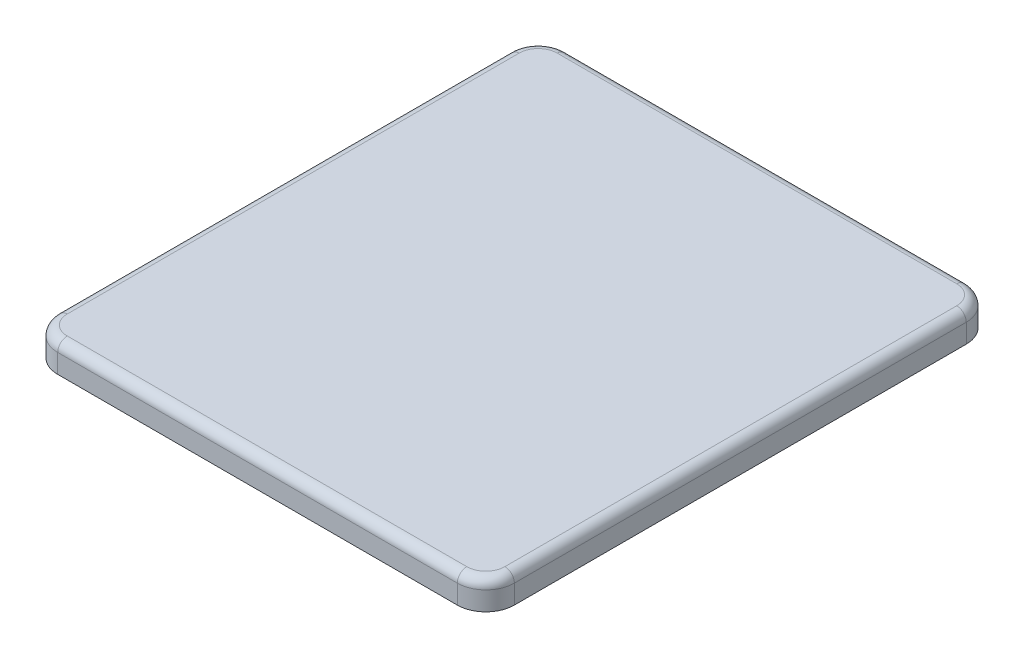
SolidWorks part; units mm, degrees
ref_plane "Front Plane" through (0, 0, 0) normal (0, 0, 1) x (1, 0, 0)
ref_plane "Top Plane" through (0, 0, 0) normal (0, 1, 0) x (1, 0, 0)
ref_plane "Right Plane" through (0, 0, 0) normal (1, 0, 0) x (0, 0, -1)
sketch "Sketch1" plane through (0, 0, 0) normal (0, 1, 0) x (1, 0, 0)
  line L1 (-24, -26.75) -> (24, -26.75)
  line L2 (-24, -26.75) -> (-24, 26.75)
  line L3 (-24, 26.75) -> (24, 26.75)
  line L4 (24, -26.75) -> (24, 26.75)
  line L5 (-24, -26.75) -> (24, 26.75) construction
  line L6 (-24, 26.75) -> (24, -26.75) construction
  point P0 (0, 0)
  dimension "D1" = 48
  dimension "D2" = 53.5
extrude "Boss-Extrude1" add sketch "Sketch1" along normal blind 3
fillet "Fillet1" radius 3 4 edges at (-24, 1.5, 26.75) (-24, 1.5, -26.75) (24, 1.5, -26.75) (24, 1.5, 26.75)
fillet "Fillet2" radius 1 8 edges at (-24, 3, 0) (-23.1213, 3, -25.8713) (0, 3, -26.75) (23.1213, 3, -25.8713) (24, 3, 0) (23.1213, 3, 25.8713) (0, 3, 26.75) (-23.1213, 3, 25.8713)
